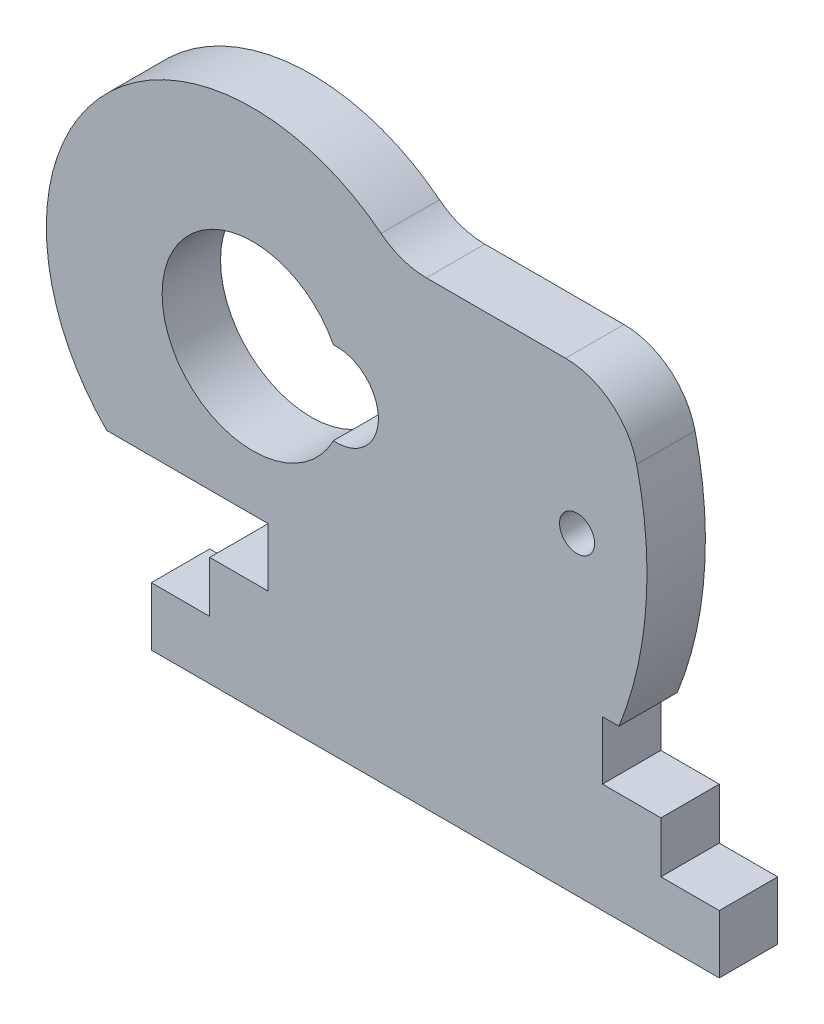
SolidWorks part; units mm, degrees
ref_plane "Front Plane" through (0, 0, 0) normal (0, 0, 1) x (1, 0, 0)
ref_plane "Top Plane" through (0, 0, 0) normal (0, 1, 0) x (1, 0, 0)
ref_plane "Right Plane" through (0, 0, 0) normal (1, 0, 0) x (0, 0, -1)
sketch "Sketch2" plane through (0, 0, 0) normal (0, 0, 1) x (1, 0, 0)
  line L0 (0, 0) -> (0, 4)
  line L1 (0, 4) -> (4, 4)
  line L2 (4, 4) -> (4, 7.5)
  line L3 (4, 7.5) -> (8, 7.5)
  line L4 (8, 7.5) -> (8, 11.5)
  line L5 (8, 11.5) -> (-3.05, 11.5)
  line L6 (-3.05, 31.5) -> (41.95, 31.5)
  line L7 (41.95, 31.5) -> (41.95, 11.5)
  line L8 (41.95, 11.5) -> (30.9, 11.5)
  line L9 (30.9, 11.5) -> (30.9, 7.5)
  line L10 (30.9, 7.5) -> (34.9, 7.5)
  line L11 (34.9, 7.5) -> (34.9, 4)
  line L12 (34.9, 4) -> (38.9, 4)
  line L13 (38.9, 4) -> (38.9, 0)
  line L14 (38.9, 0) -> (0, 0)
  line L15 (-3.05, 31.5) -> (-3.05, 11.5)
  line L16 (6.95, 27.71) -> (6.95, 35.6421) construction
  line L17 (0.74, 27.71) -> (23.16, 27.71)
  line L18 (0.74, 27.71) -> (0.74, 15.29)
  line L19 (0.74, 15.29) -> (23.16, 15.29)
  line L20 (23.16, 27.71) -> (23.16, 15.29)
  circle A1 centre (6.95, 21.5) radius 14.1421
  circle A2 centre (36.95, 26.5) radius 1.5
  circle A4 centre (36.95, 26.5) radius 7.0711
  circle A5 centre (6.95, 21.5) radius 6.21
  circle A6 centre (6.95, 21.5) radius 1.5
  arc A7 (12.4721, 24.3409) -> (12.4721, 18.6591) centre (12.7, 21.5) cw
  circle A8 centre (6.95, 31.6761) radius 1.2
  circle A9 centre (29.16, 21.5) radius 1.2
  circle A11 centre (6.95, 21.5) radius 30 construction
  circle A12 centre (6.95, 21.5) radius 27
  point P2 (0.74, 21.5)
  point P3 (19.45, 0)
  point P10 (19.45, 31.5)
  point P24 (-3.05, 21.5)
  point P38 (6.95, 31.6761)
  dimension "D5" = 22.42
  dimension "D10" = 30
  dimension "D13" = 3
  dimension "D15" = 3
  dimension "D7" = 10
  dimension "D9" = 5.75
  dimension "D16" = 2.85
  dimension "D18" = 2.4
  dimension "D19" = 60
  dimension "D20" = 3
  dimension "D1" = 4
  dimension "D2" = 22.9
  dimension "D3" = 4
  dimension "D4" = 4
  dimension "D6" = 12.42
  dimension "D8" = 10
  dimension "D11" = 5
  dimension "D12" = 5
  dimension "D14" = 3.5
  dimension "D17" = 6
extrude "Boss-Extrude1" add sketch "Sketch2" along normal blind 4 contours L15 A1 | L17 A1 L6 L15 L5 L4 L19 L18 | L6 A1 | A4 L6 A1 L17 L20 L19 L4 L3 L2 L1 L0 L14 L13 L12 L11 L10 L9 L8 L7 | A5 L17 L18 | A5 A7 L19 A1 L17 | A1 L19 L20 L17 | A5 L18 L19 | A8 L16 A1 L6 | L16 L17 A1 L6 A8 | A4 A12 L6 | A12 L14 L13 L12 L11 L10 L9
fillet "Fillet1" radius 5 2 edges at (16.95, 31.5, 2) (32.0299, 31.5, 2)
